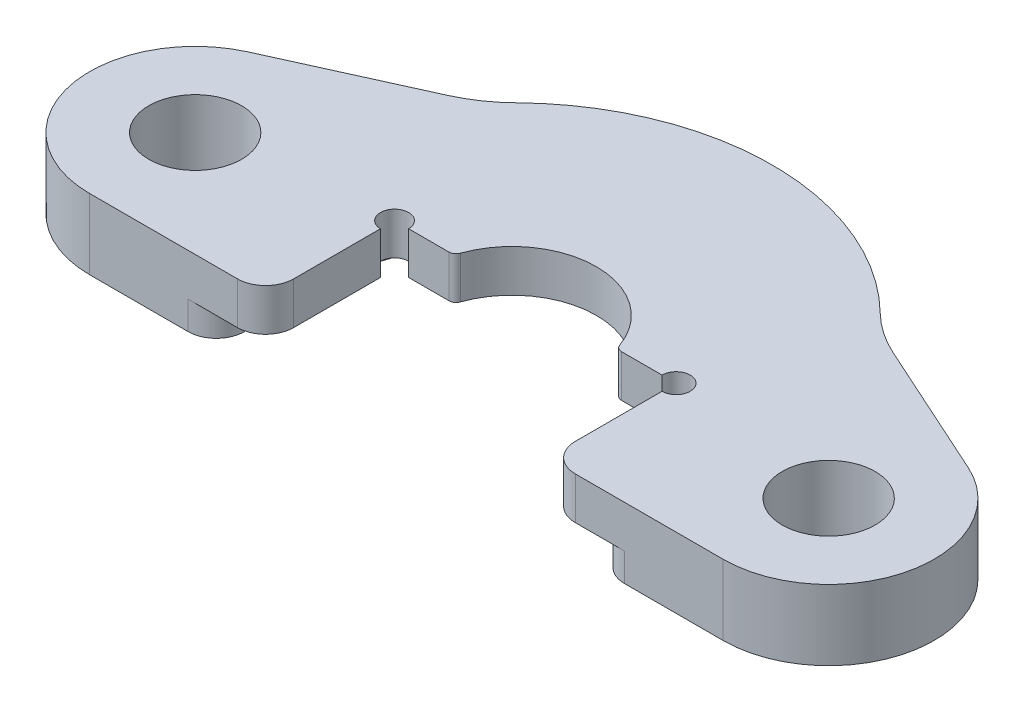
SolidWorks part; units mm, degrees
material "SS400"
ref_plane "Front Plane" through (0, 0, 0) normal (0, 0, 1) x (1, 0, 0)
ref_plane "Top Plane" through (0, 0, 0) normal (0, 1, 0) x (1, 0, 0)
ref_plane "Right Plane" through (0, 0, 0) normal (1, 0, 0) x (0, 0, -1)
sketch "Sketch1" plane through (0, 0, 0) normal (0, 1, 0) x (1, 0, 0)
  line L0 (-25.5905, 6.8336) -> (-14.0253, 12.0641)
  line L5 (25.5905, 6.8336) -> (14.0253, 12.0641)
  line L7 (22.5, -7.5) -> (-22.5, -7.5)
  arc A0 (14.0253, 12.0641) -> (-14.0253, 12.0641) centre (0, 0) ccw
  arc A7 (-25.5905, 6.8336) -> (-22.5, -7.5) centre (-22.5, 0) ccw
  arc A9 (22.5, -7.5) -> (25.5905, 6.8336) centre (22.5, 0) ccw
  dimension "D1" = 15
extrude "Boss-Extrude1" add sketch "Sketch1" along normal blind 5
sketch "Sketch2" plane through (0, 5, 0) normal (0, 1, 0) x (1, 0, 0)
  line L0 (10, -7.5) -> (10, 1.6615)
  line L3 (-22.5, -7.5) -> (22.5, -7.5) construction
  line L4 (10, 1.6615) -> (5.7654, 1.6615)
  line L5 (-5.7654, 1.6615) -> (-10, 1.6615)
  line L6 (-10, 1.6615) -> (-10, -7.5)
  line L7 (-10, -7.5) -> (10, -7.5)
  arc A3 (5.7654, 1.6615) -> (-5.7654, 1.6615) centre (0, 0) ccw
  dimension "D3" = 6
extrude "Cut-Extrude1" cut sketch "Sketch2" against normal through all
fillet "Fillet1" radius 10 2 edges at (-14.0253, 2.5, -12.0641) (14.0253, 2.5, -12.0641)
hole_wizard "M6 Clearance Hole1" positions "Sketch3" profile "Sketch4" hole size "M6" standard "ANSI Metric" end condition through all
sketch "Sketch3" plane through (0, 5, 0) normal (0, 1, 0) x (1, 0, 0)
  point P0 (-22.5, 0)
  point P3 (22.5, 0)
sketch "Sketch4" plane through (-22.5, 5, 0) normal (1, 0, 0) x (0, 0, 1)
  line L0 (0, 0) -> (0, 5)
  line L1 (0, 5) -> (3.3, 5)
  line L2 (3.3, 5) -> (3.3, 0)
  line L5 (3.3, 0) -> (0, 0)
  line L11 (0, -6.35) -> (0, 107.95) construction
  dimension "Thru Hole Dia." = 6.6
  dimension "Thru Hole Depth" = 5
fillet "Fillet2" radius 0.5 2 edges at (5.7654, 2.5, -1.6615) (-5.7654, 2.5, -1.6615)
sketch "Sketch5" plane through (0, 5, 0) normal (0, 1, 0) x (1, 0, 0)
  circle A0 centre (-10, 1.6615) radius 1
  circle A1 centre (10, 1.6615) radius 1
  dimension "D1" = 2
extrude "Cut-Extrude2" cut sketch "Sketch5" against normal through all
fillet "Fillet3" radius 2 2 edges at (10, 2.5, 7.5) (-10, 2.5, 7.5)
sketch "Sketch6" plane through (0, 0, 0) normal (0, -1, 0) x (1, 0, 0)
  line L0 (0, 0) -> (0, 12) construction
  line L1 (-13.5, 0) -> (-13.5, 12)
  line L2 (13.5, 0) -> (13.5, 12)
  arc A1 (-13.5, 0) -> (13.5, 0) centre (0, 0) ccw
  arc A2 (13.5, 12) -> (-13.5, 12) centre (0, 12) ccw
  point P3 (0, 6)
  dimension "D1" = 12
  dimension "D2" = 27
extrude "Cut-Extrude3" cut sketch "Sketch6" against normal blind 2
fillet "Fillet4" radius 2 2 edges at (-13.5, 1, 7.5) (13.5, 1, 7.5)
